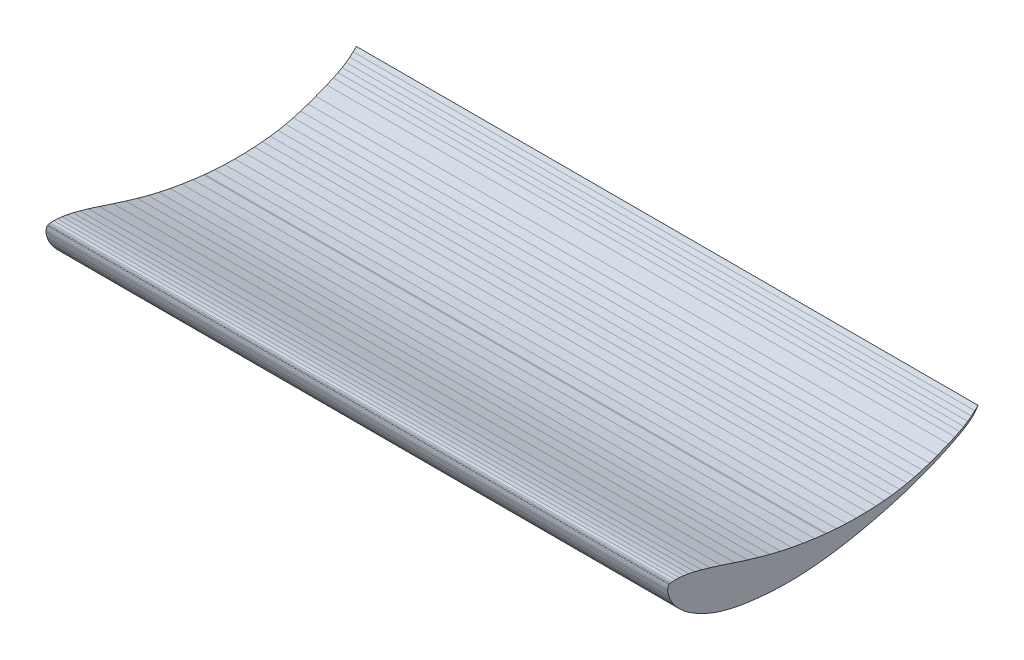
SolidWorks part; units mm, degrees
ref_plane "Front Plane" through (0, 0, 0) normal (0, 0, 1) x (1, 0, 0)
ref_plane "Top Plane" through (0, 0, 0) normal (0, 1, 0) x (1, 0, 0)
ref_plane "Right Plane" through (0, 0, 0) normal (1, 0, 0) x (0, 0, -1)
sketch "Sketch1" plane through (0, 0, -500) normal (1, 0, 0) x (0, 0, -1)
  line L0 (-642.7794, 256.1205) -> (-644.9144, 255.9046)
  line L1 (-644.9144, 255.9046) -> (-646.2003, 255.7113)
  line L2 (-646.2003, 255.7113) -> (-646.6854, 255.59)
  line L3 (-646.6854, 255.59) -> (-647.1015, 255.439)
  line L4 (-647.1015, 255.439) -> (-647.4255, 255.2746)
  line L5 (-647.4255, 255.2746) -> (-647.7146, 255.0774)
  line L6 (-647.7146, 255.0774) -> (-647.9785, 254.8392)
  line L7 (-647.9785, 254.8392) -> (-648.2754, 254.49)
  line L8 (-648.2754, 254.49) -> (-648.6362, 253.9342)
  line L9 (-648.6362, 253.9342) -> (-649.1237, 252.9299)
  line L10 (-649.1237, 252.9299) -> (-649.31, 252.4629)
  line L11 (-649.31, 252.4629) -> (-649.7663, 250.9543)
  line L12 (-649.7663, 250.9543) -> (-650.0215, 249.4233)
  line L13 (-650.0215, 249.4233) -> (-650.0943, 247.7798)
  line L14 (-650.0943, 247.7798) -> (-650.0387, 246.6055)
  line L15 (-650.0387, 246.6055) -> (-649.6027, 243.6994)
  line L16 (-649.6027, 243.6994) -> (-648.4417, 239.4745)
  line L17 (-648.4417, 239.4745) -> (-647.3535, 236.322)
  line L18 (-647.3535, 236.322) -> (-645.4226, 231.7286)
  line L19 (-645.4226, 231.7286) -> (-643.0513, 227.3571)
  line L20 (-643.0513, 227.3571) -> (-640.1205, 222.9387)
  line L21 (-640.1205, 222.9387) -> (-636.5684, 218.4052)
  line L22 (-636.5684, 218.4052) -> (-632.2649, 213.6789)
  line L23 (-632.2649, 213.6789) -> (-627.3261, 208.9819)
  line L24 (-627.3261, 208.9819) -> (-621.7615, 204.3594)
  line L25 (-621.7615, 204.3594) -> (-615.5216, 199.7954)
  line L26 (-615.5216, 199.7954) -> (-608.5486, 195.2715)
  line L27 (-608.5486, 195.2715) -> (-600.7289, 190.7686)
  line L28 (-600.7289, 190.7686) -> (-596.0054, 188.3052)
  line L29 (-596.0054, 188.3052) -> (-587.1844, 184.1604)
  line L30 (-587.1844, 184.1604) -> (-577.9172, 180.3716)
  line L31 (-577.9172, 180.3716) -> (-568.1377, 176.927)
  line L32 (-568.1377, 176.927) -> (-557.8889, 173.8602)
  line L33 (-557.8889, 173.8602) -> (-547.1805, 171.1891)
  line L34 (-547.1805, 171.1891) -> (-536.0187, 168.915)
  line L35 (-536.0187, 168.915) -> (-534.4442, 168.6308)
  line L36 (-534.4442, 168.6308) -> (-521.6502, 166.6048)
  line L37 (-521.6502, 166.6048) -> (-508.136, 164.9088)
  line L38 (-508.136, 164.9088) -> (-492.4306, 163.3903)
  line L39 (-492.4306, 163.3903) -> (-475.8521, 162.3334)
  line L40 (-475.8521, 162.3334) -> (-459.8967, 161.8848)
  line L41 (-459.8967, 161.8848) -> (-444.5108, 162.0041)
  line L42 (-444.5108, 162.0041) -> (-429.1007, 162.6446)
  line L43 (-429.1007, 162.6446) -> (-413.2324, 163.8168)
  line L44 (-413.2324, 163.8168) -> (-396.3324, 165.6016)
  line L45 (-396.3324, 165.6016) -> (-379.4187, 167.905)
  line L46 (-379.4187, 167.905) -> (-361.881, 170.8008)
  line L47 (-361.881, 170.8008) -> (-343.6547, 174.3153)
  line L48 (-343.6547, 174.3153) -> (-324.6385, 178.4838)
  line L49 (-324.6385, 178.4838) -> (-304.6972, 183.3614)
  line L50 (-304.6972, 183.3614) -> (-286.8492, 188.2034)
  line L51 (-286.8492, 188.2034) -> (-270.1058, 193.2229)
  line L52 (-270.1058, 193.2229) -> (-252.5151, 199.0672)
  line L53 (-252.5151, 199.0672) -> (-235.9484, 205.1653)
  line L54 (-235.9484, 205.1653) -> (-219.8513, 211.678)
  line L55 (-219.8513, 211.678) -> (-204.1689, 218.6163)
  line L56 (-204.1689, 218.6163) -> (-191.3088, 224.7823)
  line L57 (-191.3088, 224.7823) -> (-180.7527, 230.2866)
  line L58 (-180.7527, 230.2866) -> (-173.5559, 234.3681)
  line L59 (-173.5559, 234.3681) -> (-168.3213, 237.6592)
  line L60 (-168.3213, 237.6592) -> (-163.91, 240.8742)
  line L61 (-163.91, 240.8742) -> (-160.165, 244.1407)
  line L62 (-160.165, 244.1407) -> (-156.561, 247.9825)
  line L63 (-156.561, 247.9825) -> (-153.3366, 252.1745)
  line L64 (-153.3366, 252.1745) -> (-150.914, 255.9513)
  line L65 (-150.914, 255.9513) -> (-156.0197, 250.9041)
  line L66 (-156.0197, 250.9041) -> (-161.5018, 246.2262)
  line L67 (-161.5018, 246.2262) -> (-167.4193, 241.8659)
  line L68 (-167.4193, 241.8659) -> (-173.7237, 237.8688)
  line L69 (-173.7237, 237.8688) -> (-180.4222, 234.1876)
  line L70 (-180.4222, 234.1876) -> (-187.9795, 230.5382)
  line L71 (-187.9795, 230.5382) -> (-198.5735, 226.0028)
  line L72 (-198.5735, 226.0028) -> (-216.1458, 219.0947)
  line L73 (-216.1458, 219.0947) -> (-228.6327, 214.5088)
  line L74 (-228.6327, 214.5088) -> (-240.6391, 210.5729)
  line L75 (-240.6391, 210.5729) -> (-252.2487, 207.256)
  line L76 (-252.2487, 207.256) -> (-264.6821, 204.2653)
  line L77 (-264.6821, 204.2653) -> (-276.9338, 201.8828)
  line L78 (-276.9338, 201.8828) -> (-289.2791, 200.034)
  line L79 (-289.2791, 200.034) -> (-301.6965, 198.6889)
  line L80 (-301.6965, 198.6889) -> (-314.9274, 197.7073)
  line L81 (-314.9274, 197.7073) -> (-329.9306, 197.0339)
  line L82 (-329.9306, 197.0339) -> (-346.4396, 196.8177)
  line L83 (-346.4396, 196.8177) -> (-362.6577, 197.1593)
  line L84 (-362.6577, 197.1593) -> (-378.5665, 198.0411)
  line L85 (-378.5665, 198.0411) -> (-394.4655, 199.4314)
  line L86 (-394.4655, 199.4314) -> (-396.3655, 199.6292)
  line L87 (-396.3655, 199.6292) -> (-413.7072, 201.7232)
  line L88 (-413.7072, 201.7232) -> (-431.4537, 204.3586)
  line L89 (-431.4537, 204.3586) -> (-450.357, 207.7044)
  line L90 (-450.357, 207.7044) -> (-468.4657, 211.4883)
  line L91 (-468.4657, 211.4883) -> (-485.6527, 215.6411)
  line L92 (-485.6527, 215.6411) -> (-502.897, 220.3079)
  line L93 (-502.897, 220.3079) -> (-521.4832, 225.8116)
  line L94 (-521.4832, 225.8116) -> (-541.9112, 232.3104)
  line L95 (-541.9112, 232.3104) -> (-564.2867, 239.6617)
  line L96 (-564.2867, 239.6617) -> (-582.0441, 245.2544)
  line L97 (-582.0441, 245.2544) -> (-595.6891, 249.1799)
  line L98 (-595.6891, 249.1799) -> (-606.6372, 251.9717)
  line L99 (-606.6372, 251.9717) -> (-616.0607, 253.9786)
  line L100 (-616.0607, 253.9786) -> (-624.2573, 255.3132)
  line L101 (-624.2573, 255.3132) -> (-631.5376, 256.0767)
  line L102 (-631.5376, 256.0767) -> (-637.5386, 256.3177)
  line L103 (-637.5386, 256.3177) -> (-642.7794, 256.1205)
extrude "Boss-Extrude3" add sketch "Sketch1" along normal blind 1000
ref_plane "Plane2" through (1010, 0, 0) normal (1, 0, 0) x (0, 0, -1)
